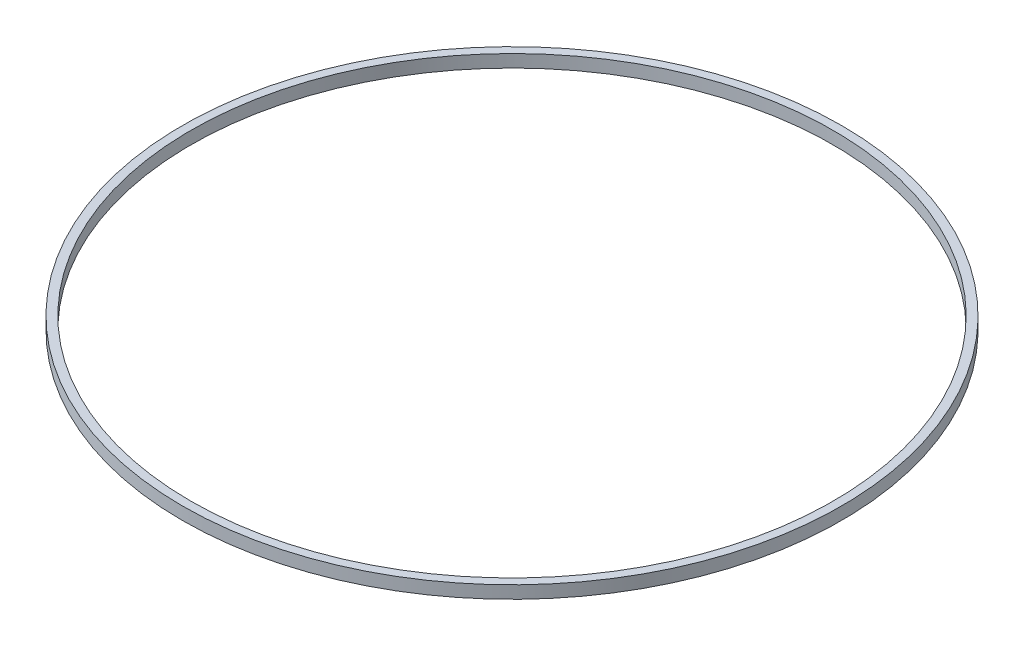
SolidWorks part; units mm, degrees
ref_plane "Front Plane" through (0, 0, 0) normal (0, 0, 1) x (1, 0, 0)
ref_plane "Top Plane" through (0, 0, 0) normal (0, 1, 0) x (1, 0, 0)
ref_plane "Right Plane" through (0, 0, 0) normal (1, 0, 0) x (0, 0, -1)
sketch "Sketch1" plane through (0, 0, 0) normal (0, 1, 0) x (1, 0, 0)
  circle A2 centre (0, 0) radius 78.5
  dimension "D1" = 157
extrude "Boss-Extrude1" add sketch "Sketch1" along normal blind 3
sketch "Sketch2" plane through (0, 3, 0) normal (0, 1, 0) x (1, 0, 0)
  circle A0 centre (0, 0) radius 76.5
  dimension "D1" = 153
extrude "Cut-Extrude1" cut sketch "Sketch2" against normal through all both and the other way through all
